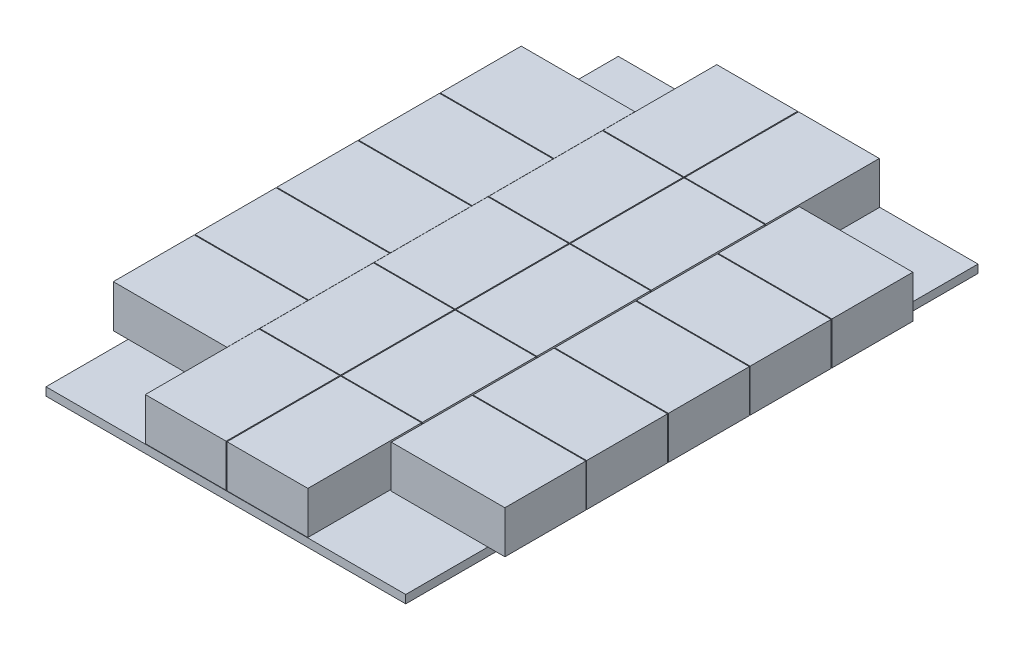
SolidWorks part; units mm, degrees
ref_plane "Front Plane" through (0, 0, 0) normal (0, 0, 1) x (1, 0, 0)
ref_plane "Top Plane" through (0, 0, 0) normal (0, 1, 0) x (1, 0, 0)
ref_plane "Right Plane" through (0, 0, 0) normal (1, 0, 0) x (0, 0, -1)
sketch "Sketch1" plane through (0, 0, 0) normal (0, 1, 0) x (1, 0, 0)
  line L1 (-110, -175) -> (110, -175)
  line L2 (-110, -175) -> (-110, 175)
  line L3 (-110, 175) -> (110, 175)
  line L4 (110, -175) -> (110, 175)
  line L5 (-110, -175) -> (110, 175) construction
  line L6 (-110, 175) -> (110, -175) construction
  point P0 (0, 0)
  dimension "D1" = 220
  dimension "D2" = 350
extrude "Boss-Extrude1" add sketch "Sketch1" along normal blind 5
sketch "Sketch2" plane through (0, 5, 0) normal (0, 1, 0) x (1, 0, 0)
  line L0 (0, 0) -> (-110, 0) construction
  line L1 (-110, 175) -> (-110, -175) construction
  line L2 (-110, 0) -> (0, 0) construction
  line L3 (0, 0) -> (0, 175) construction
  line L4 (110, 175) -> (-110, 175) construction
  line L6 (-0.1, -34.75) -> (-49.5, -34.75)
  line L7 (-0.1, -34.75) -> (-0.1, 34.75)
  line L8 (-0.1, 34.75) -> (-49.5, 34.75)
  line L9 (-49.5, -34.75) -> (-49.5, 34.75)
  line L10 (-0.1, -34.75) -> (-49.5, 34.75) construction
  line L11 (-0.1, 34.75) -> (-49.5, -34.75) construction
  point P5 (-24.8, 0)
  dimension "D1" = 0.1
  dimension "D2" = 49.5
  dimension "D3" = 69.5
extrude "Boss-Extrude2" add sketch "Sketch2" along normal blind 26
pattern_linear "LPattern1" count 2 spacing 50 along (1, 0, 0) of "Boss-Extrude2"
pattern_linear "LPattern3" count 3 spacing 70 along (0, 0, -1) count 3 spacing 70 along (0, 0, 1) of "Boss-Extrude2", "LPattern1"
sketch "Sketch4" plane through (0, 5, 0) normal (0, 1, 0) x (1, 0, 0)
  line L0 (0, 0) -> (-142.4786, 0) construction
  line L1 (-49.5, 34.75) -> (-49.5, -34.75) construction
  line L2 (-119.1, -24.75) -> (-49.6, -24.75)
  line L3 (-119.1, -24.75) -> (-119.1, 24.75)
  line L4 (-119.1, 24.75) -> (-49.6, 24.75)
  line L5 (-49.6, -24.75) -> (-49.6, 24.75)
  line L6 (-119.1, -24.75) -> (-49.6, 24.75) construction
  line L7 (-119.1, 24.75) -> (-49.6, -24.75) construction
  point P3 (-84.35, 0)
  dimension "D1" = 0.1
  dimension "D2" = 69.5
  dimension "D3" = 49.5
extrude "Boss-Extrude3" add sketch "Sketch4" along normal blind 26
pattern_linear "LPattern4" count 3 spacing 50 along (0, 0, 1) count 3 spacing 50 along (0, 0, -1) of "Boss-Extrude3"
pattern_linear "LPattern5" count 2 spacing 170 along (1, 0, 0) of "LPattern4", "Boss-Extrude3"
